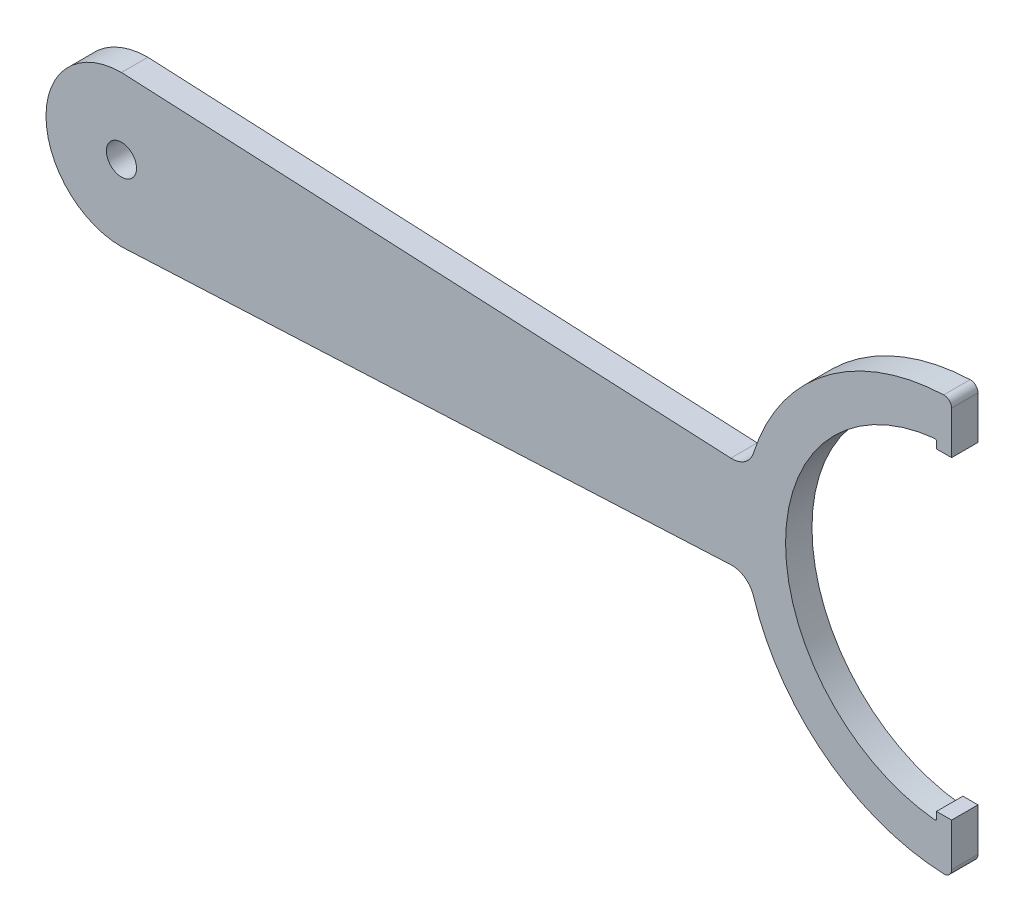
SolidWorks part; units mm, degrees
ref_plane "Plan de face" through (0, 0, 0) normal (0, 0, 1) x (1, 0, 0)
ref_plane "Plan de dessus" through (0, 0, 0) normal (0, 1, 0) x (1, 0, 0)
ref_plane "Plan de droite" through (0, 0, 0) normal (1, 0, 0) x (0, 0, -1)
sketch "Esquisse1" plane through (0, 0, 0) normal (0, 0, 1) x (1, 0, 0)
  line L0 (0, 0) -> (110, 0) construction
  line L1 (110, 36.4848) -> (110, -54.5011) construction
  line L2 (108, 36.4848) -> (108, -50.7188) construction
  line L3 (0, 10) -> (83.1625, 6)
  line L4 (0, -10) -> (83.1625, -6)
  line L5 (113, 36.4848) -> (113, -54.5011) construction
  line L6 (110, 20.7945) -> (110, 27.5)
  line L7 (110, 20.7945) -> (108, 20.7945)
  line L8 (108, 20.7945) -> (108, 21.9089)
  line L10 (110, -20.7945) -> (108, -20.7945)
  line L11 (108, -20.7945) -> (108, -21.9089)
  line L14 (110, -20.7945) -> (110, -27.5)
  arc A0 (0, 10) -> (0, -10) centre (0, 0) ccw
  arc A1 (83.1625, -6) -> (110, -27.5) centre (110, 0) ccw
  arc A2 (108, 21.9089) -> (108, -21.9089) centre (110, 0) ccw
  arc A3 (110, 27.5) -> (83.1625, 6) centre (110, 0) ccw
  dimension "D1" = 20
  dimension "D2" = 55
  dimension "D3" = 110
  dimension "D4" = 44
  dimension "D5" = 2
  dimension "D6" = 3
extrude "Extrusion1" add sketch "Esquisse1" along normal blind 3.5
fillet "Congé1" radius 3 1 edges at (83.1625, 6, 1.75)
fillet "Congé2" radius 3 1 edges at (83.1625, -6, 1.75)
fillet "Congé3" radius 1 1 edges at (110, 27.5, 1.75)
fillet "Congé4" radius 1 1 edges at (110, -27.5, 1.75)
fillet "Congé7" radius 0.2 1 edges at (108, -21.9089, 1.75)
fillet "Congé8" radius 0.2 1 edges at (108, 21.9089, 1.75)
sketch "Esquisse2" plane through (0, 0, 3.5) normal (0, 0, 1) x (1, 0, 0)
  circle A0 centre (0, 0) radius 2
  dimension "D1" = 4
extrude "Extrusion2" cut sketch "Esquisse2" against normal blind 3.5
